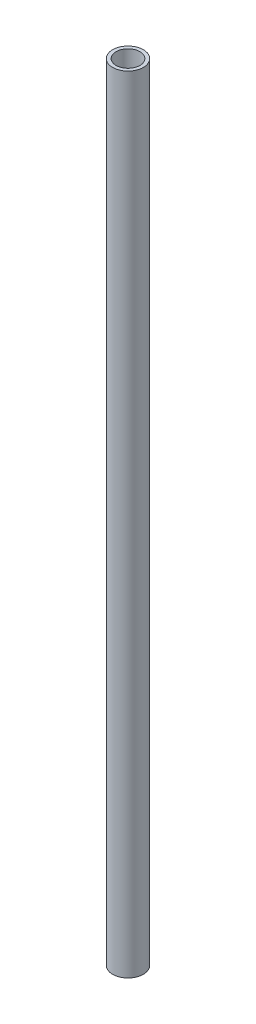
SolidWorks part; units mm, degrees
ref_plane "Front Plane" through (0, 0, 0) normal (0, 0, 1) x (1, 0, 0)
ref_plane "Top Plane" through (0, 0, 0) normal (0, 1, 0) x (1, 0, 0)
ref_plane "Right Plane" through (0, 0, 0) normal (1, 0, 0) x (0, 0, -1)
sketch "Sketch1" plane through (0, 0, 0) normal (0, 1, 0) x (1, 0, 0)
  circle A0 centre (0, 0) radius 2.25
  circle A1 centre (0, 0) radius 1.75
  dimension "D1" = 4.5
  dimension "D2" = 0.5
extrude "Boss-Extrude1" add sketch "Sketch1" along normal blind 115
